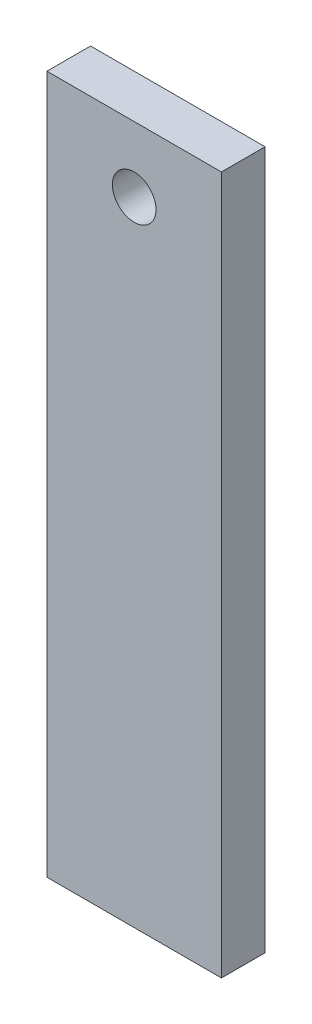
SolidWorks part; units mm, degrees
ref_plane "Front Plane" through (0, 0, 0) normal (0, 0, 1) x (1, 0, 0)
ref_plane "Top Plane" through (0, 0, 0) normal (0, 1, 0) x (1, 0, 0)
ref_plane "Right Plane" through (0, 0, 0) normal (1, 0, 0) x (0, 0, -1)
sketch "Sketch1" plane through (0, 0, 0) normal (0, 0, 1) x (1, 0, 0)
  line L1 (-25.4, 0) -> (25.4, 0)
  line L2 (-25.4, 0) -> (-25.4, 203.2)
  line L3 (-25.4, 203.2) -> (25.4, 203.2)
  line L4 (25.4, 0) -> (25.4, 203.2)
  dimension "D1" = 50.8
  dimension "D2" = 203.2
extrude "Boss-Extrude1" add sketch "Sketch1" along normal blind 12.7
hole_wizard "1/4-20 Tapped Hole1" positions "Sketch2" profile "Sketch3" tap size "1/4-20" standard "ANSI Inch"
sketch "Sketch2" plane through (0, 0, 0) normal (0, -1, 0) x (-1, 0, 0)
  line L0 (0, 0) -> (0, -12.7) construction
  line L1 (25.4, -12.7) -> (-25.4, -12.7) construction
  point P0 (15.875, -6.35)
  point P2 (-15.875, -6.35)
  point P14 (0, 0)
  point P15 (0, -6.35)
  point P16 (0, 0)
  dimension "D1" = 31.75
sketch "Sketch3" plane through (-15.875, 0, 6.35) normal (1, 0, 0) x (0, 0, -1)
  line L0 (0, 0) -> (0, 26.9338)
  line L1 (0, 26.9338) -> (2.5527, 25.4)
  line L2 (2.5527, 25.4) -> (2.5527, 0)
  line L5 (2.5527, 0) -> (0, 0)
  line L10 (0, 26.9338) -> (-2.5527, 25.4) construction
  line L11 (0, -6.35) -> (0, 107.95) construction
  dimension "Tap Drill Dia." = 5.1054
  dimension "Tap Drill Depth" = 25.4
  dimension "Drill Angle" = 118
cosmetic thread "Hole Thread1"
cosmetic thread "Hole Thread2"
sketch "Sketch4" plane through (0, 0, 0) normal (0, 0, -1) x (-1, 0, 0)
  line L0 (0, 184.15) -> (25.4, 184.15) construction
  line L1 (25.4, 203.2) -> (25.4, 0) construction
  line L2 (0, 184.15) -> (0, 203.2) construction
  line L3 (-25.4, 203.2) -> (25.4, 203.2) construction
  circle A0 centre (0, 184.15) radius 6.35
  point P2 (0, 177.8)
  dimension "D1" = 12.7
  dimension "D2" = 19.05
extrude "Cut-Extrude1" cut sketch "Sketch4" against normal through all
